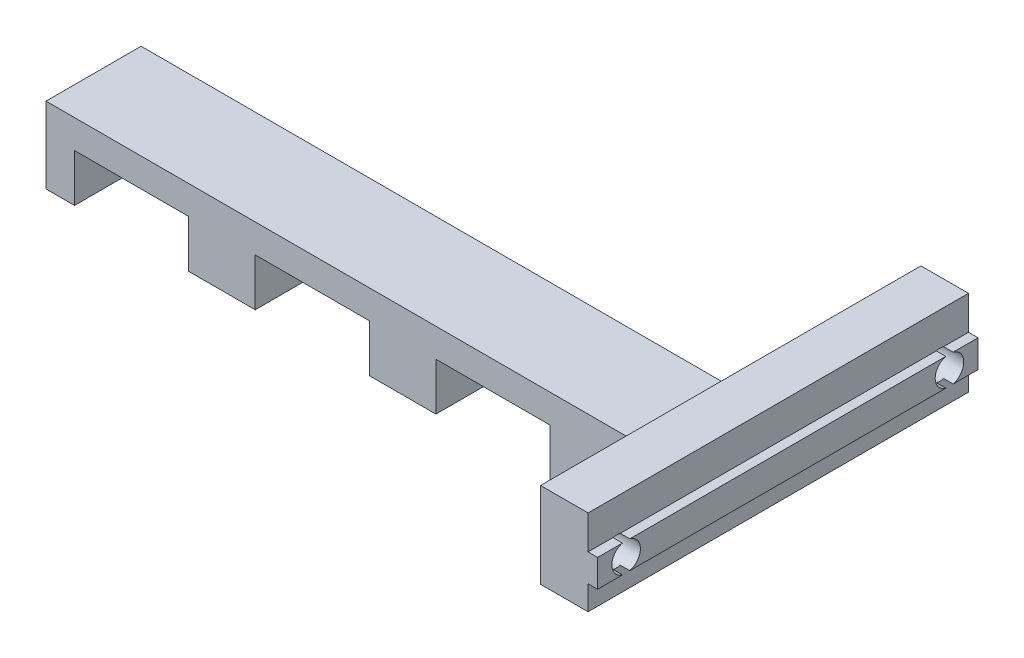
SolidWorks part; units mm, degrees
ref_plane "Front Plane" through (0, 0, 0) normal (0, 0, 1) x (1, 0, 0)
ref_plane "Top Plane" through (0, 0, 0) normal (0, 1, 0) x (1, 0, 0)
ref_plane "Right Plane" through (0, 0, 0) normal (1, 0, 0) x (0, 0, -1)
sketch "Esquisse1" plane through (0, 0, 0) normal (0, 0, 1) x (1, 0, 0)
  line L0 (3, 0) -> (3, 5)
  line L1 (3, 5) -> (15, 5)
  line L2 (15, 5) -> (15, 0)
  line L3 (15, 0) -> (22, 0)
  line L4 (22, 0) -> (22, 5)
  line L5 (22, 5) -> (34, 5)
  line L6 (34, 5) -> (34, 0)
  line L7 (34, 0) -> (41, 0)
  line L8 (41, 0) -> (41, 5)
  line L9 (41, 5) -> (53, 5)
  line L10 (53, 5) -> (53, 0)
  line L11 (53, 0) -> (60, 0)
  line L12 (72, 5) -> (72, 8)
  line L13 (72, 8) -> (0, 8)
  line L14 (0, 8) -> (0, 0)
  line L15 (0, 0) -> (3, 0)
  line L16 (60, 0) -> (60, 5)
  line L17 (60, 5) -> (72, 5)
  point P18 (71.3324, 9)
  dimension "D2" = 12
  dimension "D3" = 12
  dimension "D4" = 12
  dimension "D5" = 3
  dimension "D6" = 12
  dimension "D7" = 8
  dimension "D8" = 3
  dimension "D9" = 7
  dimension "D10" = 7
  dimension "D11" = 7
extrude "Main" add sketch "Esquisse1" along normal mid plane 10
sketch "Sketch1" plane through (0, 0, 0) normal (0, 0, 1) x (1, 0, 0)
  line L0 (67, 14) -> (72, 14)
  line L2 (72, 14) -> (72, 10.45)
  line L4 (72, 10.45) -> (73, 10.45)
  line L5 (73, 10.45) -> (73, 7.55)
  line L6 (73, 7.55) -> (72, 7.55)
  line L7 (72, 7.55) -> (72, 5)
  line L8 (72, 5) -> (67, 5)
  line L10 (67, 5) -> (67, 14)
  line L11 (60, 5) -> (72, 5) construction
  point P2 (67.8095, 30.8001)
  point P3 (71.7015, 9.7902)
  point P5 (67, 12)
  point P7 (72, 12)
  point P8 (0, 0)
  point P15 (0, 0)
  point P16 (76.7081, 0)
  point P17 (81.4671, -0.1866)
  point P18 (72, 9)
  dimension "D1" = 5
  dimension "D2" = 2.9
  dimension "D3" = 2.55
  dimension "D4" = 1
  dimension "D5" = 9
  dimension "D6" = 3.55
extrude "MakerBeamFix" add sketch "Sketch1" along normal mid plane 40
sketch "Sketch2" plane through (73, 0, 0) normal (1, 0, 0) x (0, 0, -1)
  line L0 (-20, 7.55) -> (-20, 10.45) construction
  line L1 (20, 7.55) -> (20, 10.45) construction
  circle A0 centre (-17, 9) radius 1.5
  circle A1 centre (17, 9) radius 1.5
  point P4 (-20, 9)
  dimension "D3" = 3
  dimension "D1" = 3
  dimension "D2" = 3
  dimension "D4" = 34
extrude "MakerBeamFixHole" cut sketch "Sketch2" against normal blind 30
fillet "Fillet1" radius 2 3 edges at (67, 6.5, -5) (67, 6.5, 5) (67, 8, 0)
